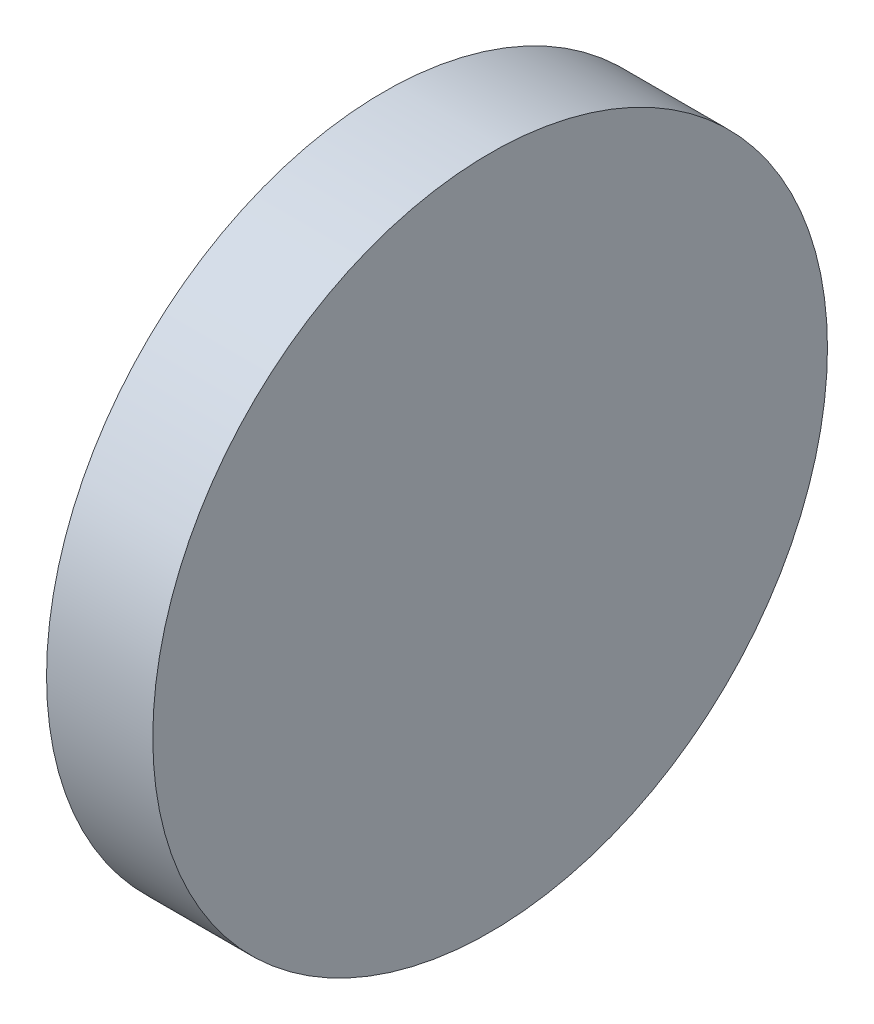
SolidWorks part; units mm, degrees
ref_plane "前视基准面" through (0, 0, 0) normal (0, 0, 1) x (1, 0, 0)
ref_plane "上视基准面" through (0, 0, 0) normal (0, 1, 0) x (1, 0, 0)
ref_plane "右视基准面" through (0, 0, 0) normal (1, 0, 0) x (0, 0, -1)
sketch "草图1" plane through (0, 0, 0) normal (0, 0, 1) x (1, 0, 0)
  line L0 (0, 6.35) -> (0, 0)
  line L2 (0, 6.35) -> (2, 6.35)
  line L3 (0, 0) -> (2, 0)
  line L4 (2, 6.35) -> (2, 0)
  dimension "D1" = 6.35
  dimension "D2" = 2
revolve "旋转2" add sketch "草图1" angle 360 about L3
